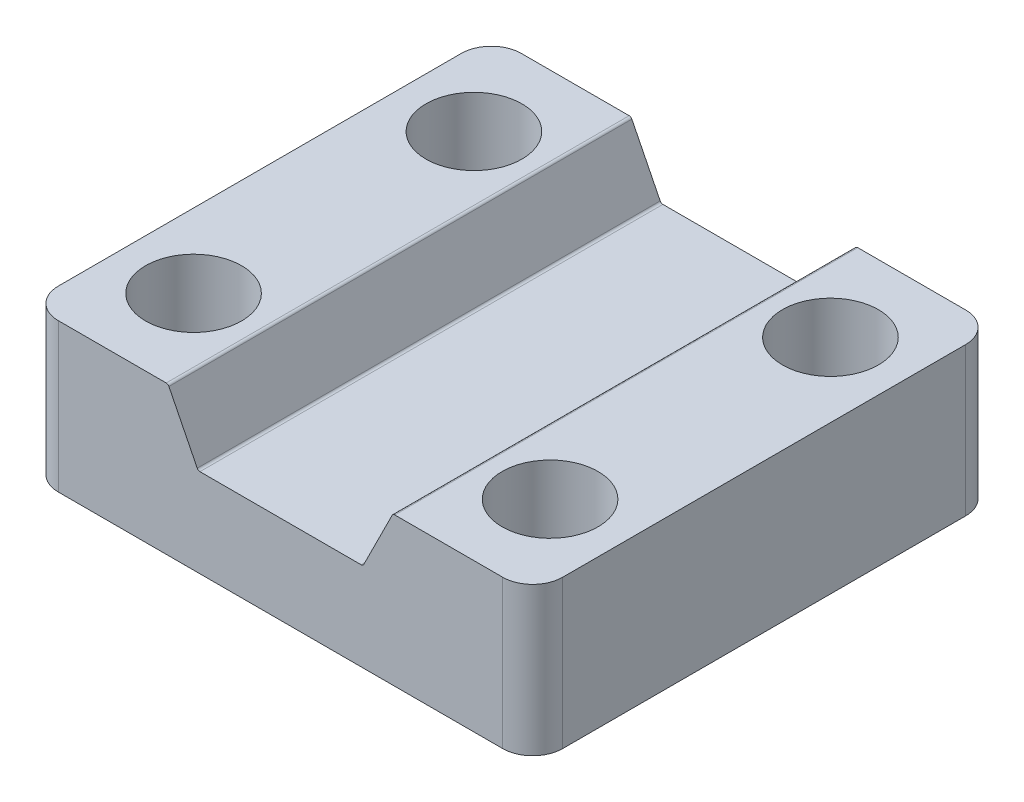
SolidWorks part; units mm, degrees
ref_plane "Front Plane" through (0, 0, 0) normal (0, 0, 1) x (1, 0, 0)
ref_plane "Top Plane" through (0, 0, 0) normal (0, 1, 0) x (1, 0, 0)
ref_plane "Right Plane" through (0, 0, 0) normal (1, 0, 0) x (0, 0, -1)
sketch "Sketch1" plane through (0, 0, 0) normal (0, 1, 0) x (1, 0, 0)
  line L0 (-15.1003, 11.8745) -> (15.1003, 11.8745) construction
  line L1 (-15.1003, 11.8745) -> (-15.1003, -11.8745) construction
  line L2 (-15.1003, -11.8745) -> (15.1003, -11.8745) construction
  line L3 (15.1003, 11.8745) -> (15.1003, -11.8745) construction
  line L4 (15.1003, 11.8745) -> (-15.1003, -11.8745) construction
  line L6 (-21.3614, 19.6088) -> (21.3614, 19.6088)
  line L7 (-21.3614, 19.6088) -> (-21.3614, -19.6088)
  line L8 (-21.3614, -19.6088) -> (21.3614, -19.6088)
  line L9 (21.3614, 19.6088) -> (21.3614, -19.6088)
  line L10 (-21.3614, 19.6088) -> (21.3614, -19.6088) construction
  line L11 (-21.3614, -19.6088) -> (21.3614, 19.6088) construction
  circle A0 centre (15.1003, -11.8745) radius 4.064
  circle A1 centre (-15.1003, 11.8745) radius 4.064
  circle A2 centre (15.1003, 11.8745) radius 4.064
  circle A3 centre (-15.1003, -11.8745) radius 4.064
  point P8 (0, -11.8745)
  point P9 (15.1003, 0)
  point P10 (0, 0)
  point P11 (0, 0)
  dimension "D1" = 8.128
  dimension "D2" = 15.621
  dimension "D3" = 22.0726
  dimension "D4" = 42.7228
  dimension "D5" = 39.2176
extrude "Boss-Extrude1" add sketch "Sketch1" along normal blind 12.573
sketch "Sketch2" plane through (0, 0, 19.6088) normal (0, 0, 1) x (1, 0, 0)
  line L0 (-9.525, 12.573) -> (-6.985, 7.493)
  line L1 (-21.3614, 12.573) -> (21.3614, 12.573) construction
  line L2 (-6.985, 7.493) -> (6.985, 7.493)
  line L3 (6.985, 7.493) -> (9.525, 12.573)
  line L4 (-9.525, 12.573) -> (9.525, 12.573)
  point P4 (0, 7.493)
  point P7 (0, 12.573)
  dimension "D1" = 5.08
  dimension "D2" = 13.97
  dimension "D3" = 19.05
extrude "Cut-Extrude1" cut sketch "Sketch2" against normal through all both and the other way through all
fillet "Fillet1" radius 0.254 4 edges at (6.985, 7.493, 0) (9.525, 12.573, 0) (-6.985, 7.493, 0) (-9.525, 12.573, 0)
fillet "Fillet2" radius 2.54 4 edges at (21.3614, 6.2865, -19.6088) (-21.3614, 6.2865, -19.6088) (21.3614, 6.2865, 19.6088) (-21.3614, 6.2865, 19.6088)
